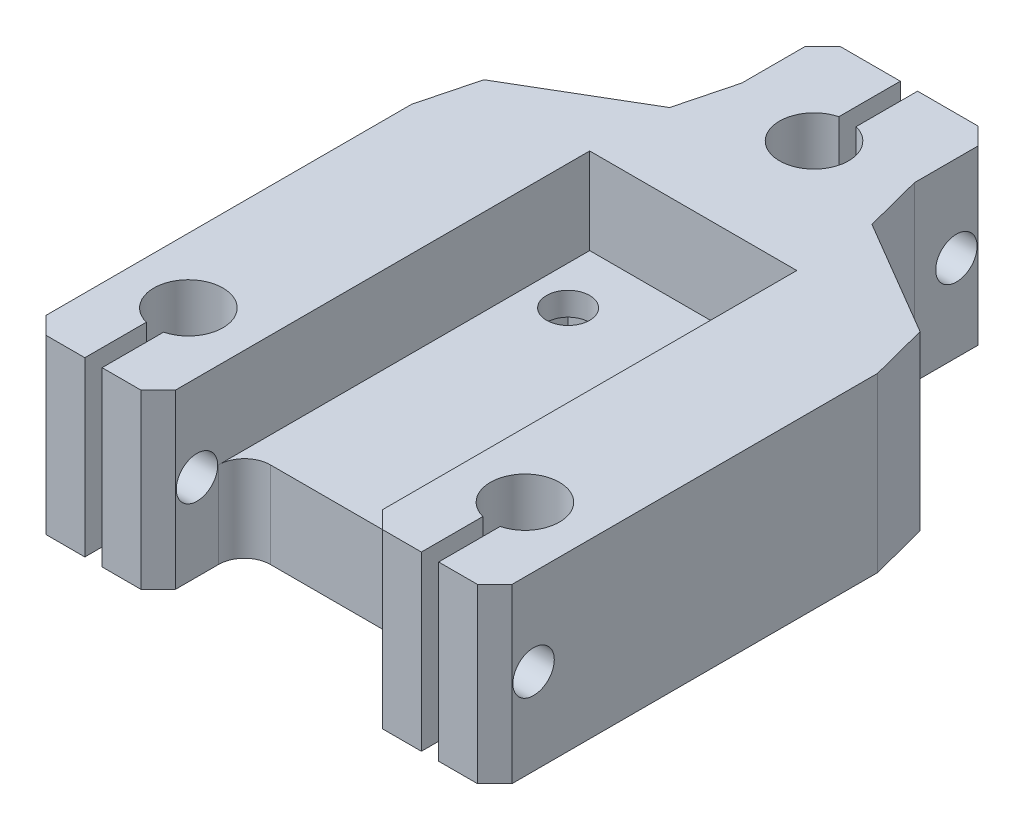
SolidWorks part; units mm, degrees
ref_plane "Front Plane" through (0, 0, 0) normal (0, 0, 1) x (1, 0, 0)
ref_plane "Top Plane" through (0, 0, 0) normal (0, 1, 0) x (1, 0, 0)
ref_plane "Right Plane" through (0, 0, 0) normal (1, 0, 0) x (0, 0, -1)
sketch "Sketch1" plane through (0, 0, 0) normal (0, 1, 0) x (1, 0, 0)
  line L0 (7.5, 13) -> (-7.5, 13) construction
  line L1 (-12, 20) -> (12, 20)
  line L2 (-12, 20) -> (-12, -20)
  line L3 (-12, -20) -> (12, -20)
  line L4 (12, 20) -> (12, -20)
  line L5 (-12, 20) -> (12, -20) construction
  line L6 (-12, -20) -> (12, 20) construction
  line L7 (0, 13) -> (0, 20) construction
  circle A0 centre (7.5, 13) radius 2.5
  circle A1 centre (-7.5, 13) radius 2.5
  point P0 (0, 0)
  dimension "D3" = 5
  dimension "D4" = 15
  dimension "D1" = 24
  dimension "D2" = 40
  dimension "D5" = 7
extrude "Boss-Extrude1" add sketch "Sketch1" along normal blind 10
sketch "Sketch2" plane through (0, 0, 0) normal (0, -1, 0) x (1, 0, 0)
  line L0 (-12, -20) -> (-12, 30)
  line L5 (12, 30) -> (12, -20)
  line L6 (12, -20) -> (-12, -20)
  line L12 (-12, 30) -> (-27, 30)
  line L13 (-27, 30) -> (-27, -20)
  line L14 (-10, -45) -> (10, -45)
  line L15 (27, -20) -> (27, 30)
  line L16 (27, 30) -> (12, 30)
  line L17 (-27, -20) -> (-10, -30)
  line L18 (-10, -30) -> (-10, -45)
  line L19 (10, -45) -> (10, -30)
  line L20 (10, -30) -> (27, -20)
  line L21 (0, 0) -> (0, -45) construction
  line L22 (-19.5, 30) -> (-19.5, 19) construction
  line L23 (19.5, 19) -> (19.5, 30) construction
  circle A0 centre (0, -34) radius 4
  circle A1 centre (-19.5, 19) radius 4
  circle A2 centre (19.5, 19) radius 4
  dimension "D3" = 15
  dimension "D9" = 50
  dimension "D10" = 20
  dimension "D11" = 11
  dimension "D12" = 8
  dimension "D6" = 15
  dimension "D7" = 8
  dimension "D13" = 8
  dimension "D14" = 11
  dimension "D15" = 11
  dimension "D1" = 15
  dimension "D2" = 50
  dimension "D4" = 25
  dimension "D5" = 50
  dimension "D8" = 50
extrude "Boss-Extrude2" add sketch "Sketch2" against normal blind 20
sketch "Sketch4" plane through (0, 20, 0) normal (0, 1, 0) x (1, 0, 0)
  line L0 (27, -30) -> (12, -30) construction
  line L1 (20.5, -37.5) -> (18.5, -37.5)
  line L2 (20.5, -37.5) -> (20.5, -22.5)
  line L3 (20.5, -22.5) -> (18.5, -22.5)
  line L4 (18.5, -37.5) -> (18.5, -22.5)
  line L5 (20.5, -37.5) -> (18.5, -22.5) construction
  line L6 (20.5, -22.5) -> (18.5, -37.5) construction
  line L7 (-12, -30) -> (-27, -30) construction
  line L8 (-20.5, -37.5) -> (-18.5, -37.5)
  line L9 (-20.5, -37.5) -> (-20.5, -22.5)
  line L10 (-20.5, -22.5) -> (-18.5, -22.5)
  line L11 (-18.5, -37.5) -> (-18.5, -22.5)
  line L12 (-20.5, -37.5) -> (-18.5, -22.5) construction
  line L13 (-20.5, -22.5) -> (-18.5, -37.5) construction
  line L14 (-10, 45) -> (10, 45) construction
  line L15 (1, 37.5) -> (-1, 37.5)
  line L16 (1, 37.5) -> (1, 52.5)
  line L17 (1, 52.5) -> (-1, 52.5)
  line L18 (-1, 37.5) -> (-1, 52.5)
  line L19 (1, 37.5) -> (-1, 52.5) construction
  line L20 (1, 52.5) -> (-1, 37.5) construction
  point P0 (19.5, -30)
  point P7 (-19.5, -30)
  point P14 (0, 45)
  dimension "D1" = 15
  dimension "D2" = 2
  dimension "D3" = 15
  dimension "D4" = 2
  dimension "D5" = 15
  dimension "D6" = 2
extrude "Cut-Extrude1" cut sketch "Sketch4" against normal blind 20
sketch "Sketch5" plane through (27, 0, 0) normal (1, 0, 0) x (0, 0, -1)
  line L0 (-30, 20) -> (-30, 0) construction
  line L1 (45, 20) -> (45, 0) construction
  line L2 (-25.5, 10) -> (-30, 10) construction
  line L3 (40.5, 10) -> (45, 10) construction
  circle A0 centre (-25.5, 10) radius 2.4
  circle A1 centre (40.5, 10) radius 2.4
  dimension "D1" = 4.8
  dimension "D2" = 4.8
  dimension "D3" = 4.5
  dimension "D4" = 4.5
extrude "Cut-Extrude2" cut sketch "Sketch5" against normal blind 56
chamfer "Chamfer2" distance 2 angle 45 6 edges at (-10, 10, -45) (10, 10, -45) (27, 10, 30) (12, 10, 30) (-27, 10, 30) (-12, 10, 30)
chamfer "Chamfer3" distance 2 angle 45 4 edges at (-27, 10, -20) (27, 10, -20) (-10, 10, -30) (10, 10, -30)
fillet "Fillet2" radius 3 2 edges at (12, 5, 20) (-12, 5, 20)
sketch "Sketch6" plane through (0, 0, 0) normal (0, -1, 0) x (1, 0, 0)
  line L0 (-7.5, -13) -> (7.5, -13) construction
  line L2 (-14, -6.5) -> (14, -6.5)
  line L3 (-14, -6.5) -> (-14, -19.5)
  line L4 (-14, -19.5) -> (14, -19.5)
  line L5 (14, -6.5) -> (14, -19.5)
  line L6 (-14, -6.5) -> (14, -19.5) construction
  line L7 (-14, -19.5) -> (14, -6.5) construction
  point P4 (0, -13)
  dimension "D1" = 6.5
  dimension "D2" = 13
extrude "Cut-Extrude3" cut sketch "Sketch6" against normal blind 7.3
